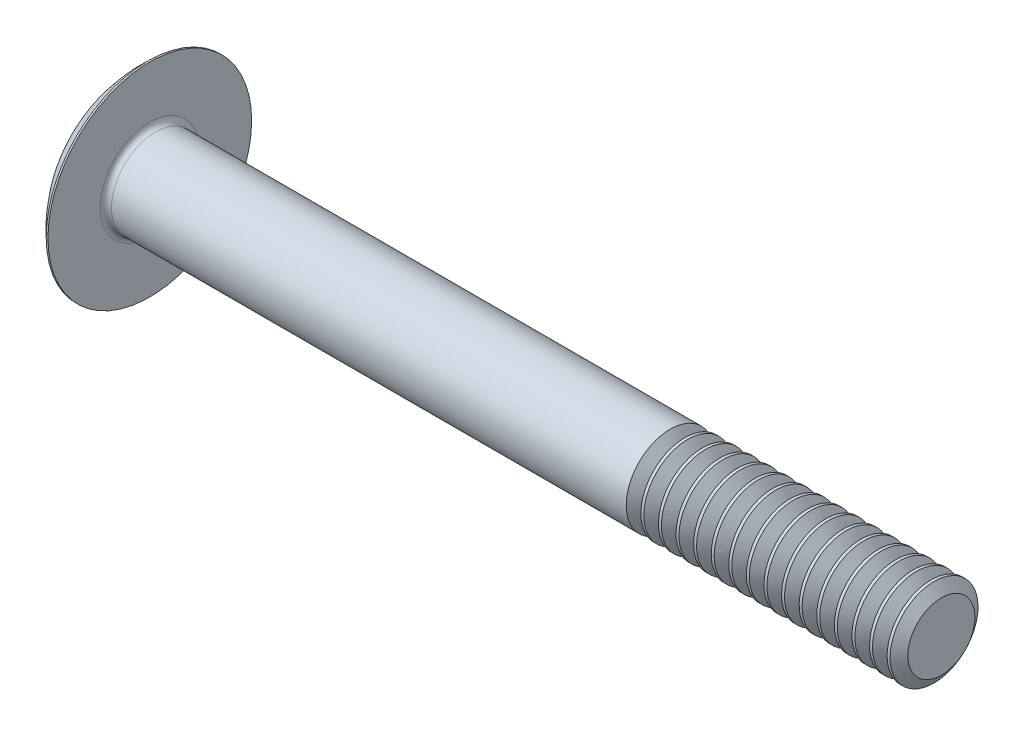
SolidWorks part; units mm, degrees
ref_plane "Plane1" through (0, 0, 0) normal (0, 0, 1) x (1, 0, 0)
ref_plane "Plane2" through (0, 0, 0) normal (0, 1, 0) x (1, 0, 0)
ref_plane "Plane3" through (0, 0, 0) normal (1, 0, 0) x (0, 0, -1)
other "Configuration Table"
sketch "BodySke" plane through (0, 0, 0) normal (0, 0, 1) x (1, 0, 0)
  line L0 (0, 0) -> (60.579, 0)
  line L1 (3.8354, 3.175) -> (60.579, 3.175)
  line L2 (3.429, -3.175) -> (60.579, -3.175) construction
  line L3 (60.579, 3.175) -> (60.579, 0)
  line L4 (3.429, -7.3533) -> (3.302, -7.3533) construction
  line L5 (3.429, 7.3533) -> (3.302, 7.3533)
  line L6 (0, 0) -> (123.825, 0) construction
  line L7 (4.699, 19.05) -> (4.699, -3.175) construction
  line L8 (3.429, 7.3533) -> (3.429, 3.5814)
  line L9 (41.529, 19.05) -> (41.529, -6.35) construction
  arc A0 (3.302, 7.3533) -> (0, 0) centre (9.8386, 0) ccw
  arc A1 (3.8354, 3.175) -> (3.429, 3.5814) centre (3.8354, 3.5814) cw
  point P11 (3.429, 3.175)
  dimension "Fillet_radius" = 0.4064
  dimension "Diameter" = 6.35
  dimension "Head_ht" = 3.429
  dimension "Length" = 57.15
  dimension "Head_dia" = 14.7066
  dimension "D1" = 0.127
  dimension "Advance" = 1.27
  dimension "Thread_nom" = 19.05
revolve "Base-Revolve" add sketch "BodySke" angle 360 about L6
cosmetic thread "ThreadCosmetic" [suppressed] parameters "Thread_length"=19.05, "Thread_minor"=4.8387
sketch "ThdSchSke" plane through (0, 0, 0) normal (0, 0, 1) x (1, 0, 0)
  line L0 (41.529, -2.4193) -> (40.9999, -3.175)
  line L1 (41.529, -2.4193) -> (42.0581, -3.175)
  line L2 (42.0581, -3.175) -> (42.0581, -3.9688)
  line L3 (-3.175, 0) -> (5.1513, 0) construction
  line L5 (42.0581, -3.9688) -> (40.9999, -3.9688)
  line L6 (40.9999, -3.9688) -> (40.9999, -3.175)
  point P6 (0, 0)
  dimension "Diameter" = 6.35
  dimension "SideAngle" = 55
  dimension "VeeAngle" = 70
  dimension "Thread_minor" = 4.8387
  dimension "Overcut" = 7.9375
  dimension "Start" = 41.529
revolve "ThreadSchematic" cut sketch "ThdSchSke" angle 360 about L3
pattern_linear "ThdSchPat" count 16 spacing 1.27 along (1, 0, 0) of "ThreadSchematic"
equation "\"Thread_length@ThreadCosmetic\" = ((sgn( (\"Length@BodySke\" - \"Advance@BodySke\" ) - \"Thread_nom@BodySke\" )-1)*( (\"Length@BodySke\" - \"Advance@BodySke\" ) - \"Thread_nom@BodySke\" ))/-2+ \"Thread_nom@BodySke\""
equation "\"Thread_minor@ThdSchSke\" = \"Thread_minor@ThreadCosmetic\""
equation "\"Diameter@ThdSchSke\" = \"Diameter@BodySke\""
equation "\"Overcut@ThdSchSke\" = \"Diameter@BodySke\" * 1.25"
equation "\"Start@ThdSchSke\" = \"Head_ht@BodySke\" + \"Length@BodySke\" - \"Thread_length@ThreadCosmetic\"  '---Non-countersunk---"
equation "\"Num_threads@ThdSchPat\" = int( \"Thread_length@ThreadCosmetic\" / \"Advance@BodySke\" + 0.999 )  + 1"
equation "\"Advance@ThdSchPat\" = \"Thread_length@ThreadCosmetic\" /  (\"Num_threads@ThdSchPat\" - 1) 'relax it"
